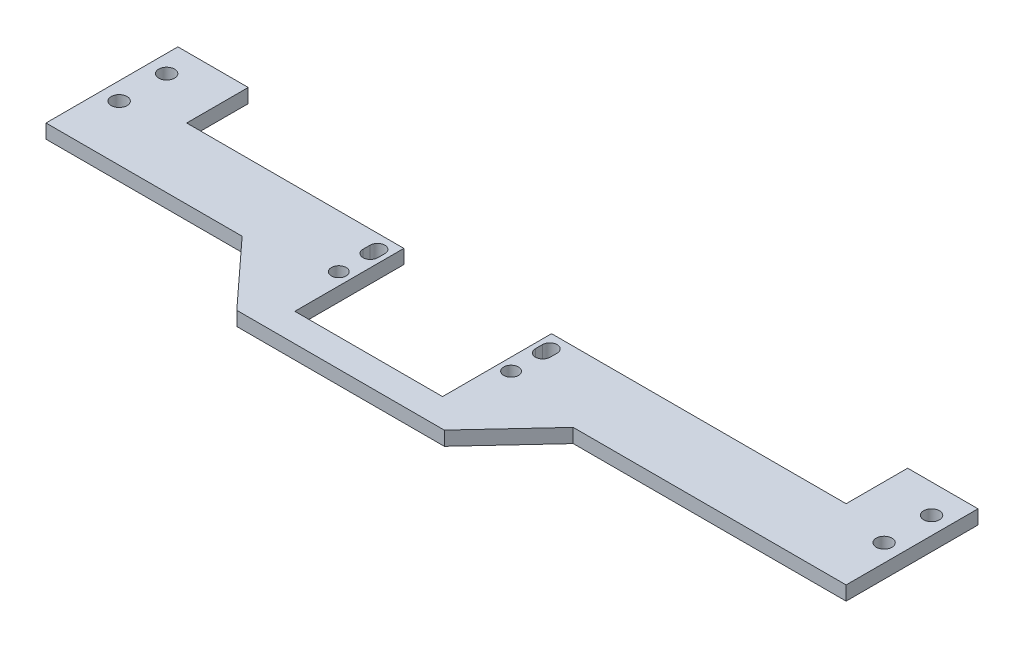
SolidWorks part; units mm, degrees
ref_plane "前视基准面" through (0, 0, 0) normal (0, 0, 1) x (1, 0, 0)
ref_plane "上视基准面" through (0, 0, 0) normal (0, 1, 0) x (1, 0, 0)
ref_plane "右视基准面" through (0, 0, 0) normal (1, 0, 0) x (0, 0, -1)
sketch "草图1" plane through (0, 0, 0) normal (0, 1, 0) x (1, 0, 0)
  line L0 (-94.1369, 29.6171) -> (-94.1369, -3.4781) construction
  line L1 (-129.6602, 20.5444) -> (-79.6369, 20.5444) construction
  line L2 (-79.6369, 20.5444) -> (-79.6369, 10.5444) construction
  line L3 (-83.1369, -5.4556) -> (-125.1369, -5.4556)
  line L4 (-128.6369, 10.5444) -> (-128.6369, 20.5444) construction
  line L5 (-79.6369, 15.5444) -> (-79.6369, 37.7054) construction
  line L6 (-79.6369, 15.5444) -> (-82.9363, 15.5444) construction
  line L7 (-133.6369, 5.5444) -> (-133.6369, -13.4556)
  line L8 (-83.1369, 25.5444) -> (-74.6369, 25.5444)
  line L9 (-81.7369, 21.5444) -> (-81.7369, 19.5444)
  line L10 (-77.5369, 21.5444) -> (-77.5369, 19.5444)
  line L11 (-104.1369, -5.4556) -> (-104.1369, 34.2079) construction
  line L12 (-130.7369, 21.5444) -> (-130.7369, 19.5444)
  line L13 (-126.5369, 21.5444) -> (-126.5369, 19.5444)
  line L14 (-83.1369, 25.5444) -> (-83.1369, -5.4556)
  line L15 (15.6131, 34.8444) -> (15.6131, 21.3444) construction
  line L16 (15.6131, 28.0444) -> (-4.9661, 28.0444) construction
  line L17 (0.6131, 43.0444) -> (20.6131, 43.0444)
  line L18 (-74.6369, 5.5444) -> (-74.6369, -13.4556)
  line L19 (-125.1369, 25.5444) -> (-125.1369, -5.4556)
  line L20 (-125.1369, 25.5444) -> (-186.8869, 25.5444)
  line L21 (20.6131, 43.0444) -> (20.6131, 13.0944)
  line L22 (-133.6369, -13.4556) -> (-74.6369, -13.4556)
  line L23 (-74.6369, 25.5444) -> (0.6131, 25.5444)
  line L24 (-74.6369, 5.5444) -> (1.2797, 5.5444)
  line L25 (0.6131, 43.0444) -> (0.6131, 25.5444)
  line L26 (1.2797, 5.5444) -> (20.6131, 5.5444)
  line L27 (20.6131, 5.5444) -> (20.6131, 13.0944)
  line L28 (-133.6369, 5.5444) -> (-189.5535, 5.5444)
  line L29 (-189.5535, 5.5444) -> (-206.8869, 5.5444)
  line L34 (-128.6369, 10.5444) -> (-79.6369, 10.5444) construction
  line L35 (-211.8869, 34.8444) -> (-199.1844, 34.8444) construction
  line L36 (-206.8869, 21.3444) -> (-193.8404, 21.3444) construction
  line L39 (-186.8869, 43.0444) -> (-186.8869, 25.5444)
  line L40 (-206.8869, 43.0444) -> (-206.8869, 5.5444)
  line L41 (-206.8869, 43.0444) -> (-186.8869, 43.0444)
  circle A0 centre (15.6131, 34.8444) radius 2.25
  circle A1 centre (15.6131, 21.3444) radius 2.25
  circle A2 centre (-79.6369, 10.5444) radius 2.1
  circle A5 centre (-128.6369, 10.5444) radius 2.1
  arc A8 (-77.5369, 21.5444) -> (-81.7369, 21.5444) centre (-79.6369, 21.5444) ccw
  arc A9 (-81.7369, 19.5444) -> (-77.5369, 19.5444) centre (-79.6369, 19.5444) ccw
  arc A10 (-126.5369, 19.5444) -> (-130.7369, 19.5444) centre (-128.6369, 19.5444) cw
  arc A11 (-130.7369, 21.5444) -> (-126.5369, 21.5444) centre (-128.6369, 21.5444) cw
  circle A12 centre (-201.8869, 34.8444) radius 2.25
  circle A13 centre (-201.8869, 21.3444) radius 2.25
  dimension "D2" = 10
  dimension "D6" = 49
  dimension "D8" = 1
  dimension "D10" = 1
  dimension "D22" = 6.7
  dimension "D25" = 5
  dimension "D26" = 112.75
  dimension "D3" = 95.25
  dimension "D4" = 14.3
  dimension "D5" = 14.5
  dimension "D7" = 49
  dimension "D9" = 5
  dimension "D11" = 24.5
  dimension "D12" = 6.8
  dimension "D13" = 3.5
  dimension "D14" = 5
  dimension "D15" = 16
  dimension "D16" = 15
  dimension "D17" = 5
  dimension "D18" = 8
  dimension "D19" = 20
  dimension "D20" = 20
  dimension "D21" = 5
  dimension "D23" = 16
  dimension "D24" = 10
  dimension "D27" = 5
  dimension "D28" = 20
extrude "凸台-拉伸1" add sketch "草图1" along normal blind 4
sketch "草图3" plane through (0, 0, 0) normal (0, -1, 0) x (1, 0, 0)
  line L0 (15.6131, -21.3444) -> (15.6131, -34.8444) construction
sketch "草图4" plane through (0, 4, 0) normal (0, 1, 0) x (1, 0, 0)
  line L0 (-133.6369, -13.4556) -> (-151.1157, 5.5444)
  line L1 (-206.8869, 5.5444) -> (-133.6369, 5.5444) construction
  line L2 (-151.1157, 5.5444) -> (-133.6369, 5.5444)
  line L3 (-133.6369, 5.5444) -> (-133.6369, -13.4556)
  line L4 (-74.6369, -13.4556) -> (-74.6369, 5.5444)
  line L5 (-74.6369, 5.5444) -> (-56.9798, 5.5444)
  line L7 (-74.6369, 5.5444) -> (20.6131, 5.5444) construction
  line L8 (-56.9798, 5.5444) -> (-74.6369, -13.4556)
extrude "凸台-拉伸2" add sketch "草图4" against normal blind 4
